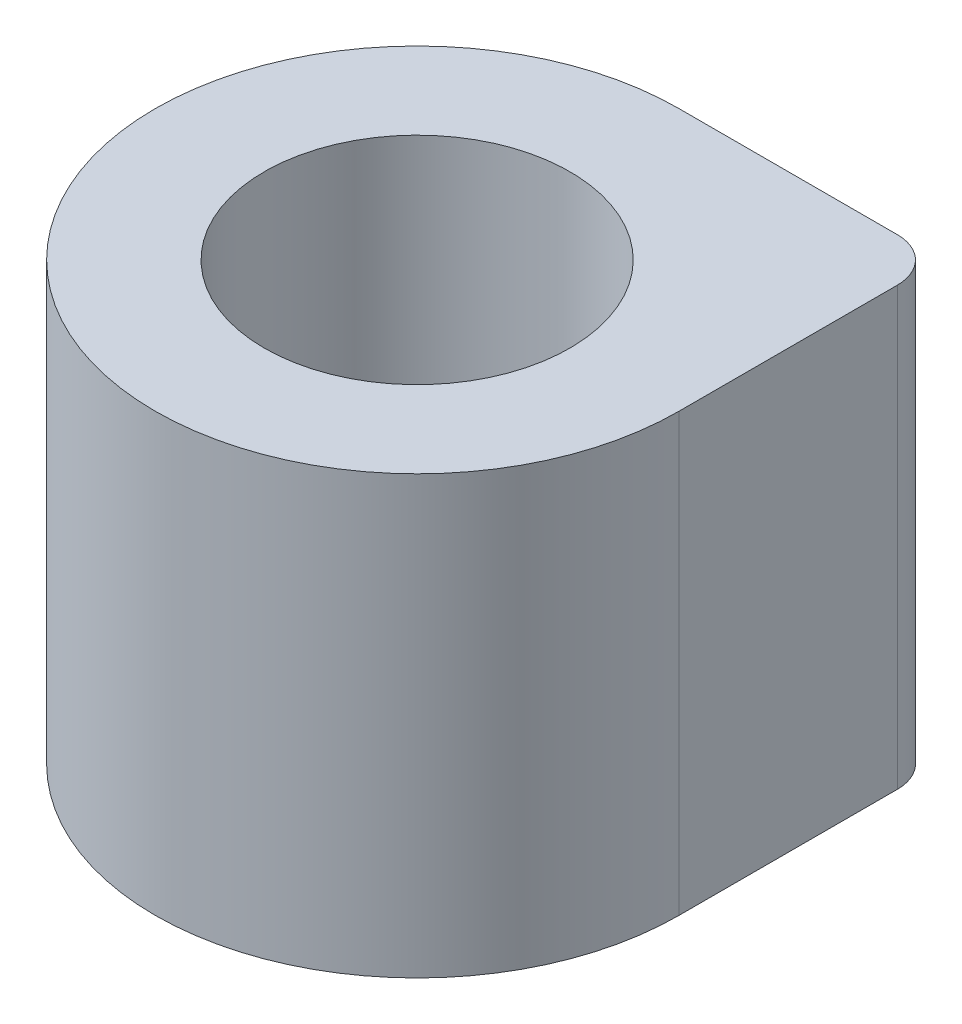
SolidWorks part; units mm, degrees
ref_plane "Front Plane" through (0, 0, 0) normal (0, 0, 1) x (1, 0, 0)
ref_plane "Top Plane" through (0, 0, 0) normal (0, 1, 0) x (1, 0, 0)
ref_plane "Right Plane" through (0, 0, 0) normal (1, 0, 0) x (0, 0, -1)
sketch "Sketch1" plane through (0, 0, 0) normal (0, 1, 0) x (1, 0, 0)
  line L0 (0, 6) -> (6, 6)
  line L1 (6, 6) -> (6, 0)
  arc A0 (0, 6) -> (6, 0) centre (0, 0) ccw
  dimension "D1" = 12
extrude "Boss-Extrude1" add sketch "Sketch1" along normal blind 10
sketch "Sketch2" plane through (0, 10, 0) normal (0, 1, 0) x (1, 0, 0)
  circle A0 centre (0, 0) radius 3.5
  dimension "D1" = 7
extrude "Cut-Extrude1" cut sketch "Sketch2" against normal blind 8
fillet "Fillet1" radius 1 1 edges at (6, 5, -6)
